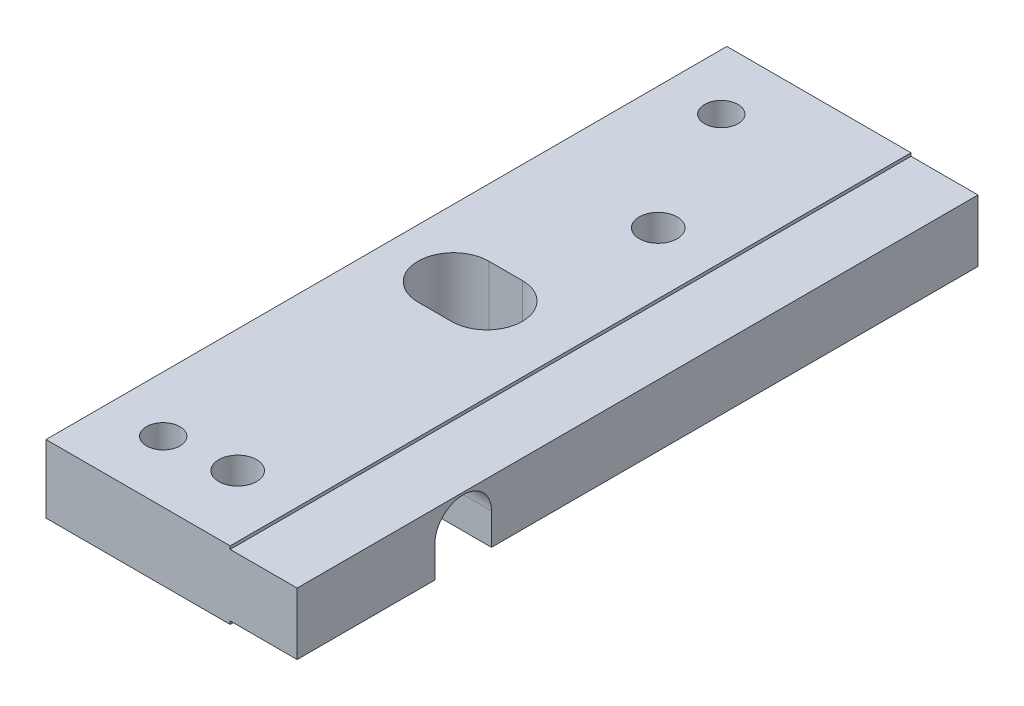
SolidWorks part; units mm, degrees
material "Generic Carbon Fiber"
ref_plane "Front Plane" through (0, 0, 0) normal (0, 0, 1) x (1, 0, 0)
ref_plane "Top Plane" through (0, 0, 0) normal (0, 1, 0) x (1, 0, 0)
ref_plane "Right Plane" through (0, 0, 0) normal (1, 0, 0) x (0, 0, -1)
sketch "Sketch1" plane through (0, 0, 0) normal (1, 0, 0) x (0, 0, -1)
  line L1 (0, -3.05) -> (61, -3.05)
  line L2 (0, -3.05) -> (0, 3.05)
  line L3 (0, 3.05) -> (61, 3.05)
  line L4 (61, -3.05) -> (61, 3.05)
  dimension "D1" = 61
  dimension "D2" = 6.1
extrude "Boss-Extrude1" add sketch "Sketch1" along normal blind 22.5
sketch "Sketch2" plane through (22.5, 0, 0) normal (1, 0, 0) x (0, 0, -1)
  line L0 (0, 3.05) -> (0, -3.05) construction
  line L1 (0, -2.775) -> (61, -2.775)
  line L2 (0, -2.775) -> (0, 2.775)
  line L3 (0, 2.775) -> (61, 2.775)
  line L4 (61, -2.775) -> (61, 2.775)
  line L5 (61, -3.05) -> (61, 3.05) construction
  line L7 (30.5, 3.05) -> (30.5, -3.05) construction
  line L8 (61, 3.05) -> (0, 3.05) construction
  line L9 (0, -3.05) -> (61, -3.05) construction
  line L10 (0, 0) -> (30.5, 0) construction
  dimension "D1" = 5.55
extrude "Cut-Extrude1" cut sketch "Sketch2" against normal blind 6 flip side to cut
sketch "Sketch5" plane through (0, 0, 0) normal (-1, 0, 0) x (0, 0, 1)
  line L0 (-14.881, 0.0496) -> (0, 0.0496) construction
  line L1 (-61, 2.775) -> (0, 2.775) construction
  line L2 (0, 3.05) -> (0, -3.05) construction
  line L3 (0, -3.05) -> (-61, -3.05) construction
  line L4 (-12.3486, 0.0496) -> (-12.3486, -3.05)
  line L5 (-12.3486, -3.05) -> (-17.4134, -3.05)
  line L6 (-17.4134, -3.05) -> (-17.4134, 0.0496)
  arc A0 (-12.3486, 0.0496) -> (-17.4134, 0.0496) centre (-14.881, 0.0496) ccw
  dimension "D1" = 5.0648
  dimension "D2" = 14.881
  dimension "D3" = 2.7254
extrude "Cut-Extrude3" cut sketch "Sketch5" against normal through all
sketch "Sketch6" plane through (0, 3.05, 0) normal (0, 1, 0) x (1, 0, 0)
  line L0 (0, 30.5) -> (22.5, 30.5) construction
  line L1 (9, 30.5) -> (6, 30.5) construction
  line L2 (22.5, 61) -> (22.5, 0) construction
  line L4 (0, 61) -> (0, 0) construction
  line L5 (9, 27.325) -> (6, 27.325)
  line L6 (9, 33.675) -> (6, 33.675)
  arc A0 (9, 27.325) -> (9, 33.675) centre (9, 30.5) ccw
  arc A1 (6, 33.675) -> (6, 27.325) centre (6, 30.5) ccw
  point P7 (7.5, 30.5)
  dimension "D2" = 3.175
  dimension "D1" = 3
  dimension "D3" = 6
extrude "Cut-Extrude4" cut sketch "Sketch6" against normal through all
sketch "Sketch7" plane through (0, 3.05, 0) normal (0, 1, 0) x (1, 0, 0)
  line L0 (5, 61) -> (5, 0) construction
  line L1 (16.5, 61) -> (0, 61) construction
  line L2 (16.5, 0) -> (0, 0) construction
  line L3 (0, 30.5) -> (22.5, 30.5) construction
  line L4 (0, 61) -> (0, 0) construction
  line L5 (22.5, 61) -> (22.5, 0) construction
  circle A0 centre (5, 55.5) radius 1.5
  circle A1 centre (5, 5.5) radius 1.5
  dimension "D1" = 3
  dimension "D2" = 5
  dimension "D3" = 25
  dimension "D4" = 25
extrude "Cut-Extrude5" cut sketch "Sketch7" against normal through all
hole_wizard "CBORE for M3 Pan Head Machine Screw2" positions "Sketch14" profile "Sketch13" counterbore size "M3" standard "ANSI Metric" end condition through all
sketch "Sketch14" plane through (0, -3.05, 0) normal (0, -1, 0) x (-1, 0, 0)
  point P0 (-11, 6.175)
  point P2 (-11, 43.85)
sketch "Sketch13" plane through (11, -3.05, -6.175) normal (1, 0, 0) x (0, 0, -1)
  line L0 (0, 0) -> (0, 6.1)
  line L1 (0, 6.1) -> (1.7, 6.1)
  line L3 (1.7, 6.1) -> (1.7, 2.2)
  line L4 (1.7, 2.2) -> (3.25, 2.2)
  line L5 (3.25, 2.2) -> (3.25, 0)
  line L7 (3.25, 0) -> (0, 0)
  line L11 (0, -6.35) -> (0, 107.95) construction
  dimension "Thru Hole Dia." = 3.4
  dimension "Thru Hole Depth" = 6.1
  dimension "C'Bore Dia." = 6.5
  dimension "C'Bore Depth" = 2.2
